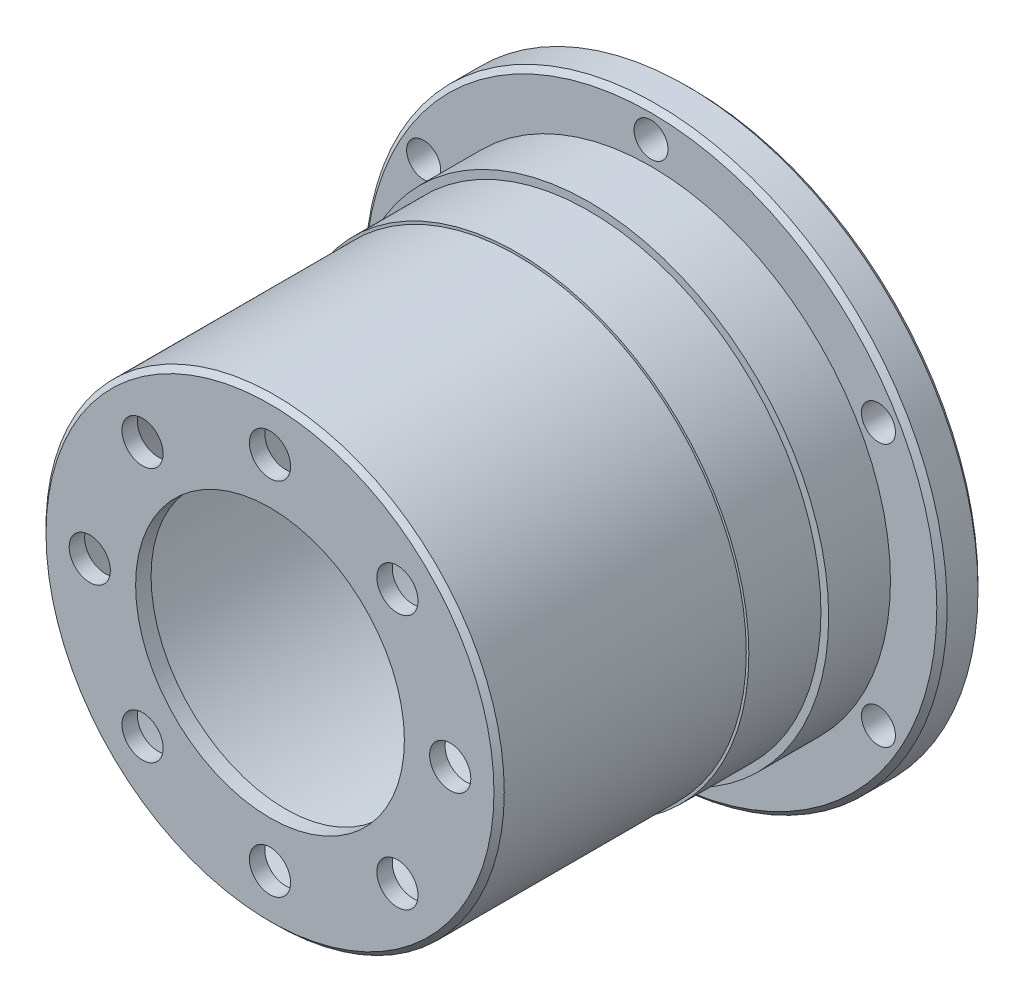
SolidWorks part; units mm, degrees
material "6061 合金"
ref_plane "前视基准面" through (0, 0, 0) normal (0, 0, 1) x (1, 0, 0)
ref_plane "上视基准面" through (0, 0, 0) normal (0, 1, 0) x (1, 0, 0)
ref_plane "右视基准面" through (0, 0, 0) normal (1, 0, 0) x (0, 0, -1)
sketch "草图1" plane through (0, 0, 0) normal (0, 0, 1) x (1, 0, 0)
  circle A0 centre (0, 0) radius 21.05
  circle A1 centre (0, 0) radius 22.25
  dimension "D1" = 42.1
  dimension "D2" = 44.5
extrude "凸台-拉伸1" add sketch "草图1" along normal blind 41
sketch "草图2" plane through (0, 0, 41) normal (0, 0, 1) x (1, 0, 0)
  circle A0 centre (0, 0) radius 13.05
  circle A1 centre (0, 0) radius 22.25
  circle A2 centre (0, 0) radius 22.25
  dimension "D2" = 26.1
  dimension "D1" = 0
extrude "凸台-拉伸2" add sketch "草图2" against normal blind 1.5
sketch "草图3" plane through (0, 0, 0) normal (0, 0, -1) x (-1, 0, 0)
  circle A0 centre (0, 0) radius 28.25
  circle A1 centre (0, 0) radius 21.05 construction
  circle A2 centre (0, 0) radius 21.05
  dimension "D1" = 56.5
extrude "凸台-拉伸3" add sketch "草图3" against normal blind 4
sketch "草图4" plane through (0, 0, 4) normal (0, 0, 1) x (1, 0, 0)
  circle A0 centre (0, 0) radius 22.25 construction
  circle A1 centre (0, 0) radius 22.25
  circle A2 centre (0, 0) radius 23.25
  dimension "D1" = 46.5
extrude "凸台-拉伸4" add sketch "草图4" along normal blind 6
sketch "草图5" plane through (0, 0, 10) normal (0, 0, 1) x (1, 0, 0)
  circle A0 centre (0, 0) radius 22.5
  circle A2 centre (0, 0) radius 22.25
  circle A3 centre (0, 0) radius 22.25 construction
  dimension "D1" = 45
extrude "凸台-拉伸5" add sketch "草图5" along normal blind 7
sketch "草图6" plane through (0, 0, 39.5) normal (0, 0, -1) x (-1, 0, 0)
  line L0 (0, 17.5) -> (0, 0) construction
  line L1 (0, 0) -> (12.3744, 12.3744) construction
  circle A0 centre (0, 0) radius 17.5 construction
  circle A1 centre (12.3744, 12.3744) radius 2
  circle A2 centre (17.5, 0) radius 2
  circle A3 centre (12.3744, -12.3744) radius 2
  circle A4 centre (0, -17.5) radius 2
  circle A5 centre (-12.3744, -12.3744) radius 2
  circle A6 centre (-17.5, 0) radius 2
  circle A7 centre (-12.3744, 12.3744) radius 2
  circle A8 centre (0, 17.5) radius 2
  point P14 (0, 0)
  dimension "D1" = 35
  dimension "D2" = 4
  dimension "D4" = 45
  dimension "D3" = 8
extrude "切除-拉伸1" cut sketch "草图6" against normal blind 7
sketch "草图7" plane through (0, 0, 4) normal (0, 0, 1) x (1, 0, 0)
  circle A0 centre (0, 0) radius 25.5 construction
  dimension "D1" = 51
hole_wizard "M4 螺纹孔1" positions "草图8" profile "草图9" tap size "M4" standard "GB"
sketch "草图8" plane through (0, 0, 4) normal (0, 0, 1) x (1, 0, 0)
  line L0 (0, 25.5) -> (0, 0) construction
  circle A0 centre (0, 0) radius 25.5 construction
  point P0 (0, 25.5)
sketch "草图9" plane through (0, 25.5, 4) normal (1, 0, 0) x (0, -1, 0)
  line L0 (0, 0) -> (0, 11.0914)
  line L1 (0, 11.0914) -> (1.65, 10.1)
  line L2 (1.65, 10.1) -> (1.65, 0)
  line L5 (1.65, 0) -> (0, 0)
  line L10 (0, 11.0914) -> (-1.65, 10.1) construction
  line L11 (0, -6.35) -> (0, 107.95) construction
  dimension "螺纹孔钻头直径" = 3.3
  dimension "螺纹孔钻头深度" = 10.1
  dimension "导头角度" = 118
cosmetic thread "孔螺蚊线1" parameters "D1"=8, "D2"=4
pattern_circular "阵列(圆周)1" count 6 over 360 about axis through (0, 0, 0) along (0, 0, 1) of "M4 螺纹孔1"
cosmetic thread "孔螺蚊线2" parameters "D1"=8, "D2"=4
cosmetic thread "孔螺蚊线3" parameters "D1"=8, "D2"=4
cosmetic thread "孔螺蚊线4" parameters "D1"=8, "D2"=4
cosmetic thread "孔螺蚊线5" parameters "D1"=8, "D2"=4
cosmetic thread "孔螺蚊线6" parameters "D1"=8, "D2"=4
chamfer "倒角1" distance 0.5 angle 45 4 edges at (21.05, 0, 0) (-28.25, 0, 0) (-28.25, 0, 4) (22.25, 0, 41)
